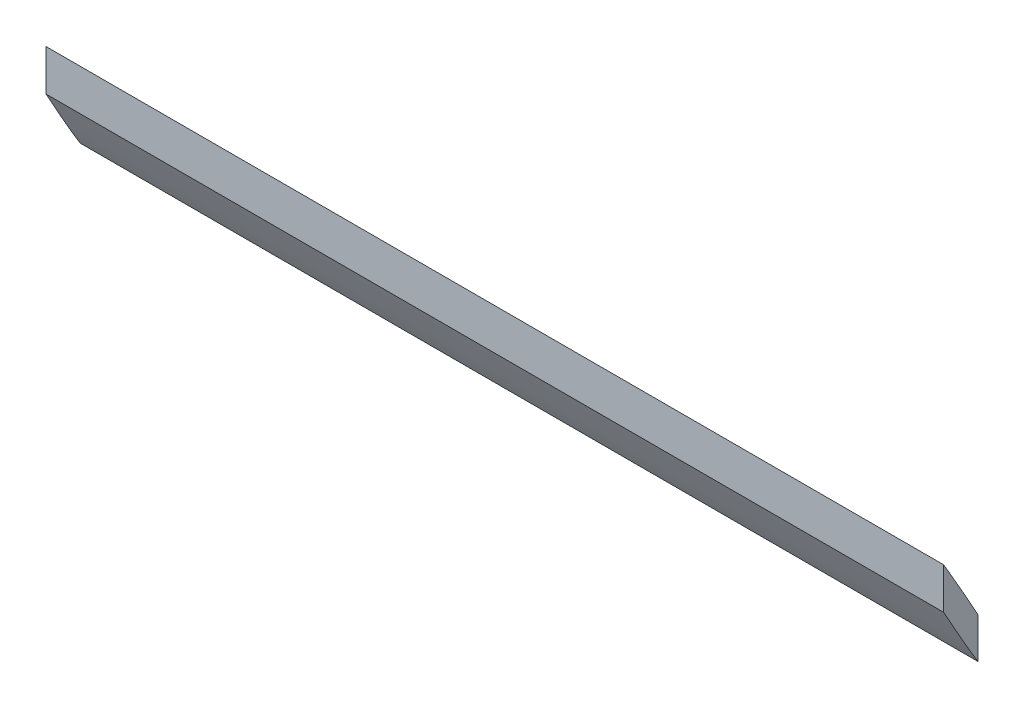
SolidWorks part; units mm, degrees
ref_plane "Front Plane" through (0, 0, 0) normal (0, 0, 1) x (1, 0, 0)
ref_plane "Top Plane" through (0, 0, 0) normal (0, 1, 0) x (1, 0, 0)
ref_plane "Right Plane" through (0, 0, 0) normal (1, 0, 0) x (0, 0, -1)
sketch "Sketch1" plane through (0, 0, 0) normal (1, 0, 0) x (0, 0, -1)
  line L4 (-93.8621, -48.2927) -> (-93.8621, -50.8152)
  line L5 (-91.7621, -51.9915) -> (-91.7621, -54.4739)
  spline S6 degree 3 poles (-91.7621, -51.9915) (-91.9683, -51.6264) (-92.1722, -51.2598) (-92.8618, -50.0207) (-93.3475, -49.1482) (-93.8621, -48.2927) knots 0.684771 0.684771 0.684771 0.684771 0.75 0.75 0.905319 0.905319 0.905319 0.905319
  spline S7 degree 3 poles (-93.8621, -50.8152) (-93.4287, -51.5901) (-93.0015, -52.3687) (-92.3003, -53.5876) (-92.0364, -54.0339) (-91.7621, -54.4739) knots 0.106259 0.106259 0.106259 0.106259 0.25 0.25 0.333978 0.333978 0.333978 0.333978
extrude "Boss-Extrude1" add sketch "Sketch1" along normal blind 55
